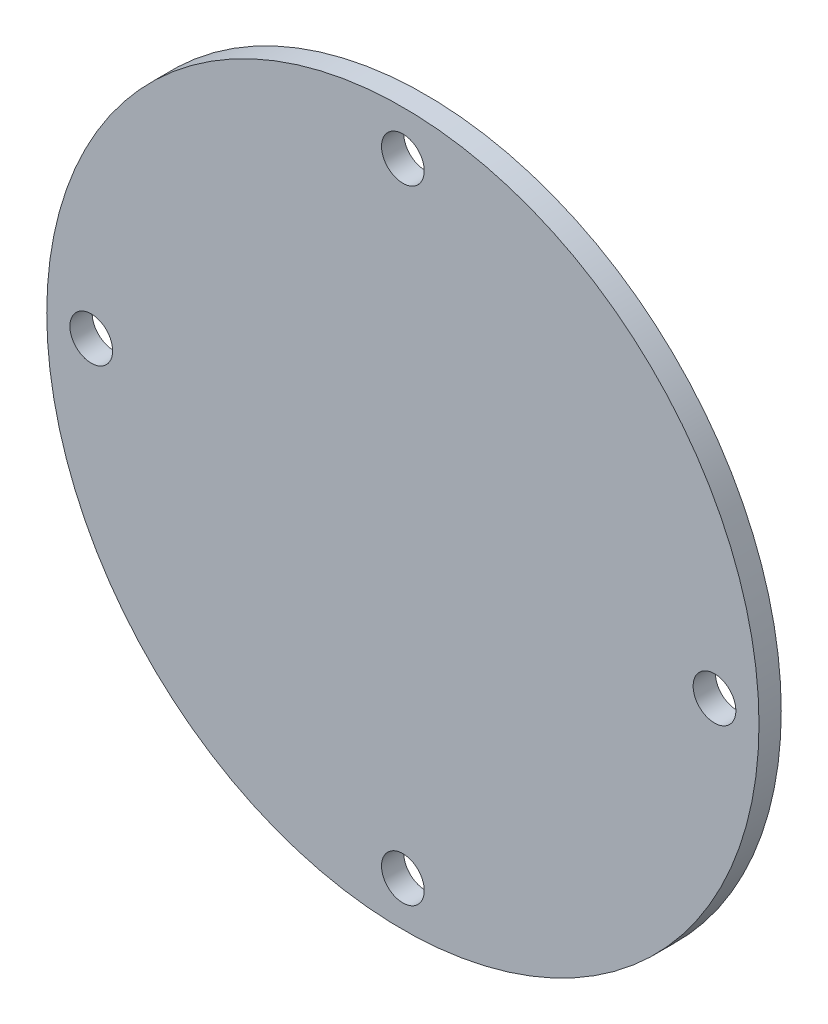
SolidWorks part; units mm, degrees
material "1060 Alloy"
ref_plane "Front Plane" through (0, 0, 0) normal (0, 0, 1) x (1, 0, 0)
ref_plane "Top Plane" through (0, 0, 0) normal (0, 1, 0) x (1, 0, 0)
ref_plane "Right Plane" through (0, 0, 0) normal (1, 0, 0) x (0, 0, -1)
sketch "Sketch1" plane through (0, 0, 0) normal (0, 0, 1) x (1, 0, 0)
  circle A0 centre (0, 0) radius 25.4
  dimension "D1" = 50.8
extrude "Boss-Extrude1" add sketch "Sketch1" along normal blind 1.5875
sketch "Sketch2" plane through (0, 0, 1.5875) normal (0, 0, 1) x (1, 0, 0)
  circle A0 centre (0, 0) radius 22.225 construction
  circle A1 centre (0, 22.225) radius 1.524
  dimension "D1" = 44.45
  dimension "D2" = 3.048
extrude "Cut-Extrude1" cut sketch "Sketch2" against normal through all
pattern_circular "CirPattern1" count 4 over 360 about axis through (0, 0, 0) along (0, 0, 1) of "Cut-Extrude1"
